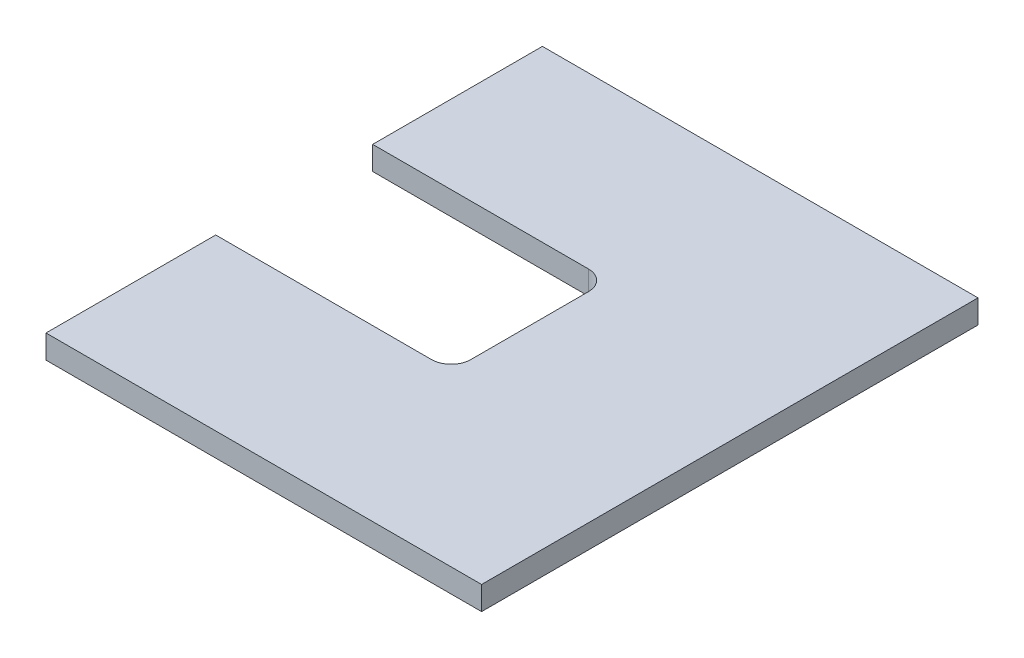
SolidWorks part; units mm, degrees
material "Acrylic (Medium-high impact)"
ref_plane "Front Plane" through (0, 0, 0) normal (0, 0, 1) x (1, 0, 0)
ref_plane "Top Plane" through (0, 0, 0) normal (0, 1, 0) x (1, 0, 0)
ref_plane "Right Plane" through (0, 0, 0) normal (1, 0, 0) x (0, 0, -1)
sketch "Sketch1" plane through (0, 0, 0) normal (0, 1, 0) x (1, 0, 0)
  line L1 (0, 0) -> (111, 0)
  line L2 (0, 0) -> (0, 126.5)
  line L3 (0, 126.5) -> (111, 126.5)
  line L4 (111, 0) -> (111, 126.5)
  dimension "D1" = 126.5
  dimension "D2" = 111
extrude "Boss-Extrude1" add sketch "Sketch1" along normal blind 6
sketch "Sketch2" plane through (0, 6, 0) normal (0, 1, 0) x (1, 0, 0)
  line L0 (0, 126.5) -> (0, 0) construction
  line L1 (0, 83.25) -> (60, 83.25)
  line L2 (0, 83.25) -> (0, 43.25)
  line L3 (0, 43.25) -> (60, 43.25)
  line L4 (60, 83.25) -> (60, 43.25)
  line L5 (111, 0) -> (111, 126.5) construction
  point P8 (111, 63.25)
  point P9 (60, 63.25)
  dimension "D1" = 40
  dimension "D2" = 60
extrude "Cut-Extrude1" cut sketch "Sketch2" against normal through all
fillet "Fillet1" radius 5 2 edges at (60, 3, -43.25) (60, 3, -83.25)
